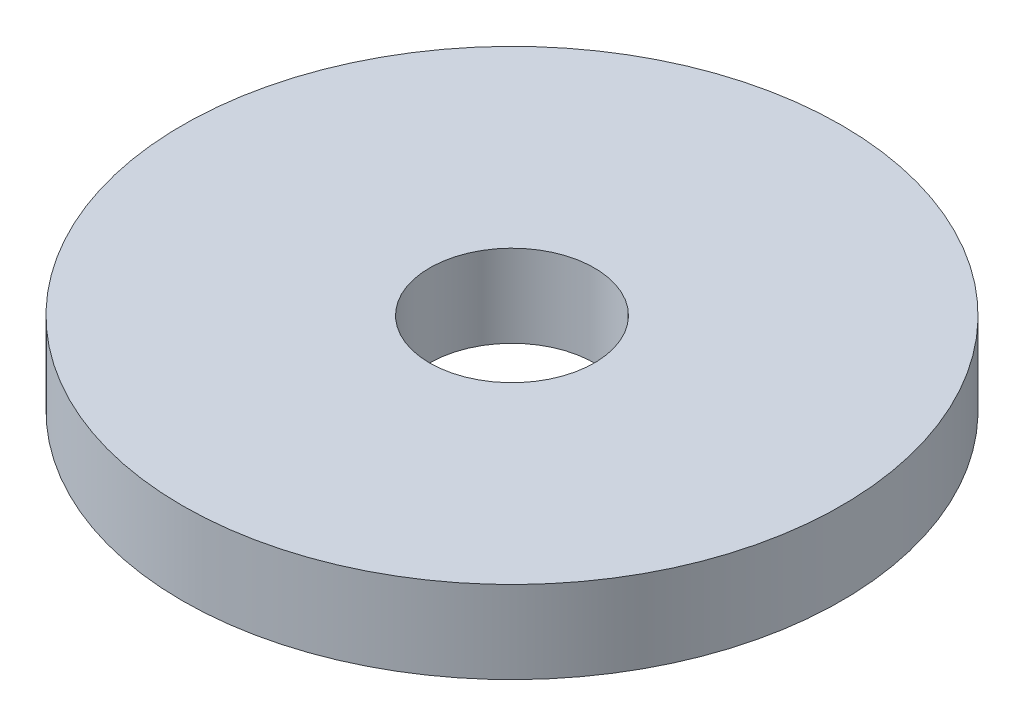
SolidWorks part; units mm, degrees
ref_plane "Front Plane" through (0, 0, 0) normal (0, 0, 1) x (1, 0, 0)
ref_plane "Top Plane" through (0, 0, 0) normal (0, 1, 0) x (1, 0, 0)
ref_plane "Right Plane" through (0, 0, 0) normal (1, 0, 0) x (0, 0, -1)
sketch "Sketch1" plane through (0, 0, 0) normal (0, 1, 0) x (1, 0, 0)
  circle A0 centre (0, 0) radius 20
  circle A1 centre (0, 0) radius 5
extrude "Boss-Extrude1" add sketch "Sketch1" along normal blind 5
